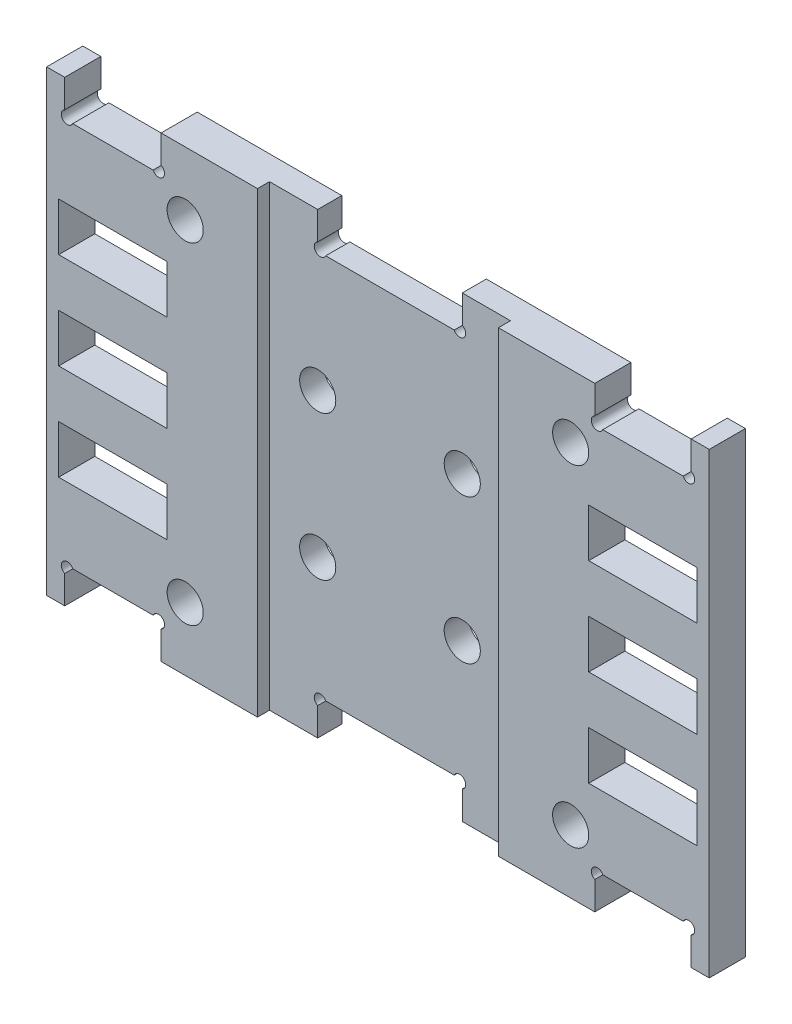
SolidWorks part; units mm, degrees
ref_plane "前视基准面" through (0, 0, 0) normal (0, 0, 1) x (1, 0, 0)
ref_plane "上视基准面" through (0, 0, 0) normal (0, 1, 0) x (1, 0, 0)
ref_plane "右视基准面" through (0, 0, 0) normal (1, 0, 0) x (0, 0, -1)
sketch "草图1" plane through (0, 0, 0) normal (0, 0, 1) x (1, 0, 0)
  line L1 (-27.5, 19) -> (27.5, 19)
  line L2 (-27.5, 19) -> (-27.5, -19)
  line L3 (-27.5, -19) -> (27.5, -19)
  line L4 (27.5, 19) -> (27.5, -19)
  line L5 (-27.5, 19) -> (27.5, -19) construction
  line L6 (-27.5, -19) -> (27.5, 19) construction
  point P0 (0, 0)
  dimension "D1" = 38
  dimension "D2" = 55
extrude "凸台-拉伸1" add sketch "草图1" along normal blind 3
sketch "草图2" plane through (0, 0, 3) normal (0, 0, 1) x (1, 0, 0)
  line L0 (-34.5256, 0) -> (42.1415, 0) construction
  line L1 (-10, -19) -> (-10, 19) construction
  line L2 (-27.5, -19) -> (27.5, -19) construction
  line L3 (27.5, 19) -> (-27.5, 19) construction
  line L4 (0, 26.7268) -> (0, -34.771) construction
  line L5 (10, -19) -> (10, 19) construction
  circle A0 centre (16, 13.75) radius 1.5
  circle A1 centre (16, -13.75) radius 1.5
  circle A2 centre (-16, 13.75) radius 1.5
  circle A3 centre (-16, -13.75) radius 1.5
  dimension "D1" = 13.75
  dimension "D2" = 3
  dimension "D3" = 10
  dimension "D4" = 6
extrude "切除-拉伸1" cut sketch "草图2" against normal blind 30
sketch "草图3" plane through (0, 0, 3) normal (0, 0, 1) x (1, 0, 0)
  line L0 (10, -19) -> (10, 19) construction
  line L1 (0, 26.7268) -> (0, -34.771) construction
  line L2 (-34.5256, 0) -> (42.1415, 0) construction
  line L3 (-10, -19) -> (-10, 19) construction
  line L4 (10, -19) -> (10, 19) construction
  line L5 (0, 26.7268) -> (0, -34.771) construction
  line L6 (-34.5256, 0) -> (42.1415, 0) construction
  line L7 (-10, -19) -> (-10, 19) construction
  line L8 (27.5, 19) -> (-27.5, 19) construction
  line L9 (27.5, -19) -> (27.5, 19) construction
  line L12 (18, 19) -> (26, 19)
  line L13 (18, 19) -> (18, 16)
  line L14 (18, 16) -> (26, 16)
  line L15 (26, 19) -> (26, 16)
  line L17 (26, -19) -> (26, -16)
  line L18 (18, -16) -> (26, -16)
  line L19 (18, -19) -> (18, -16)
  line L20 (18, -19) -> (26, -19)
  line L21 (-26, 19) -> (-26, 16)
  line L22 (-18, 16) -> (-26, 16)
  line L23 (-18, 19) -> (-18, 16)
  line L24 (-18, 19) -> (-26, 19)
  line L25 (-18, -19) -> (-26, -19)
  line L26 (-18, -19) -> (-18, -16)
  line L27 (-18, -16) -> (-26, -16)
  line L28 (-26, -19) -> (-26, -16)
  circle A0 centre (16, 13.75) radius 4 construction
  dimension "D1" = 8
  dimension "D2" = 1.5
  dimension "D3" = 8
  dimension "D4" = 3
extrude "切除-拉伸2" cut sketch "草图3" against normal blind 30
sketch "草图4" plane through (0, 0, 3) normal (0, 0, 1) x (1, 0, 0)
  line L0 (10, -19) -> (10, 19) construction
  line L1 (-10, -19) -> (-10, 19) construction
  line L2 (10, -19) -> (10, 19)
  line L3 (-10, -19) -> (-10, 19)
  line L4 (-10, -19) -> (10, -19)
  line L5 (-10, 19) -> (10, 19)
extrude "切除-拉伸3" cut sketch "草图4" against normal blind 1
sketch "草图5" plane through (0, 0, 3) normal (0, 0, 1) x (1, 0, 0)
  line L0 (36.0158, 0) -> (-43.2134, 0) construction
  line L1 (0, -26.7679) -> (0, 34.1112) construction
  line L2 (22, -14) -> (22, 14) construction
  line L3 (26.5, 6) -> (17.5, 6)
  line L4 (26.5, -2) -> (17.5, -2)
  line L5 (26.5, -2) -> (26.5, 2)
  line L6 (26.5, 2) -> (17.5, 2)
  line L7 (17.5, -2) -> (17.5, 2)
  line L8 (26.5, -2) -> (17.5, 2) construction
  line L9 (26.5, 2) -> (17.5, -2) construction
  line L10 (26.5, 6) -> (26.5, 10)
  line L11 (26.5, 6) -> (17.5, 10) construction
  line L12 (26.5, 10) -> (17.5, 6) construction
  line L13 (26.5, 10) -> (17.5, 10)
  line L14 (17.5, 6) -> (17.5, 10)
  line L15 (26.5, -10) -> (17.5, -10)
  line L16 (26.5, -10) -> (17.5, -6) construction
  line L17 (26.5, -6) -> (17.5, -6)
  line L18 (17.5, -10) -> (17.5, -6)
  line L19 (26.5, -6) -> (17.5, -10) construction
  line L20 (26.5, -10) -> (26.5, -6)
  line L21 (-26.5, -6) -> (-17.5, -10) construction
  line L22 (-26.5, -10) -> (-17.5, -6) construction
  line L23 (-26.5, 10) -> (-17.5, 6) construction
  line L24 (-26.5, 6) -> (-17.5, 10) construction
  line L25 (-26.5, 2) -> (-17.5, -2) construction
  line L26 (-26.5, -2) -> (-17.5, 2) construction
  line L27 (-26.5, -10) -> (-26.5, -6)
  line L28 (-17.5, -10) -> (-17.5, -6)
  line L29 (-26.5, -6) -> (-17.5, -6)
  line L30 (-26.5, -10) -> (-17.5, -10)
  line L31 (-17.5, 6) -> (-17.5, 10)
  line L32 (-26.5, 10) -> (-17.5, 10)
  line L33 (-26.5, 6) -> (-26.5, 10)
  line L34 (-17.5, -2) -> (-17.5, 2)
  line L35 (-26.5, 2) -> (-17.5, 2)
  line L36 (-26.5, -2) -> (-26.5, 2)
  line L37 (-26.5, -2) -> (-17.5, -2)
  line L38 (-26.5, 6) -> (-17.5, 6)
  point P9 (22, 0)
  point P14 (15, -8)
  point P35 (-15, -8)
  point P36 (-22, 0)
  dimension "D1" = 9
  dimension "D2" = 4
  dimension "D5" = 44
  dimension "D3" = 2
  dimension "D4" = 2
extrude "切除-拉伸4" cut sketch "草图5" against normal blind 10
sketch "草图6" plane through (0, 0, 2) normal (0, 0, 1) x (1, 0, 0)
  line L0 (10, 19) -> (-10, 19) construction
  line L1 (6, 16) -> (-6, 16)
  line L2 (6, 16) -> (6, 19)
  line L3 (6, 19) -> (-6, 19)
  line L4 (-6, 16) -> (-6, 19)
  line L5 (6, 16) -> (-6, 19) construction
  line L6 (6, 19) -> (-6, 16) construction
  line L7 (40.4069, 0) -> (-41.1435, 0) construction
  line L8 (6, -19) -> (-6, -16) construction
  line L9 (6, -16) -> (-6, -19) construction
  line L10 (-6, -16) -> (-6, -19)
  line L11 (6, -19) -> (-6, -19)
  line L12 (6, -16) -> (6, -19)
  line L13 (6, -16) -> (-6, -16)
  point P0 (0, 17.5)
  point P14 (0, -17.5)
  dimension "D1" = 3
  dimension "D2" = 12
extrude "切除-拉伸5" cut sketch "草图6" against normal blind 10
sketch "草图8" plane through (0, 0, 2) normal (0, 0, 1) x (1, 0, 0)
  line L0 (35.8146, 0) -> (-38.9097, 0) construction
  line L1 (0, -25.4239) -> (0, 33.2722) construction
  circle A0 centre (6, -6) radius 1.5
  circle A1 centre (6, 6) radius 1.5
  circle A2 centre (-6, 6) radius 1.5
  circle A3 centre (-6, -6) radius 1.5
  dimension "D1" = 6
  dimension "D3" = 3
  dimension "D2" = 6
extrude "切除-拉伸6" cut sketch "草图8" against normal blind 10
sketch "草图9" plane through (0, 0, 3) normal (0, 0, 1) x (1, 0, 0)
  line L0 (26, -16) -> (21.2547, -20.7453) construction
  line L1 (26, -16) -> (18, -16) construction
  line L2 (26, -16) -> (18, -16) construction
  line L3 (26, -19) -> (26, -16) construction
  line L4 (22, -16) -> (22, 6) construction
  line L5 (17.5, 6) -> (26.5, 6) construction
  line L6 (32.6576, 0) -> (-31.0257, 0) construction
  line L7 (26, 16) -> (18, 16) construction
  line L8 (0, -22.545) -> (0, 25.0951) construction
  line L9 (-26, 16) -> (-18, 16) construction
  line L10 (-22, -16) -> (-22, 6) construction
  line L11 (-26, -16) -> (-18, -16) construction
  line L12 (6, -16) -> (2.9183, -19.0817) construction
  line L13 (6, -16) -> (-6, -16) construction
  circle A0 centre (25.7879, -16.2121) radius 0.5
  circle A1 centre (18.2121, -16.2121) radius 0.5
  circle A2 centre (18.2121, 16.2121) radius 0.5
  circle A3 centre (25.7879, 16.2121) radius 0.5
  circle A4 centre (-25.7879, 16.2121) radius 0.5
  circle A5 centre (-18.2121, 16.2121) radius 0.5
  circle A6 centre (-18.2121, -16.2121) radius 0.5
  circle A7 centre (-25.7879, -16.2121) radius 0.5
  circle A8 centre (5.7879, -16.2121) radius 0.5
  circle A9 centre (-5.7879, -16.2121) radius 0.5
  circle A10 centre (-5.7879, 16.2121) radius 0.5
  circle A11 centre (5.7879, 16.2121) radius 0.5
  point P9 (26, -16.6649)
  point P23 (26, 16.6649)
  point P40 (-26, 16.6649)
  point P41 (-26, -16.6649)
  dimension "D1" = 1
  dimension "D4" = 45
  dimension "D2" = 45
  dimension "D3" = 0.3
  dimension "D5" = 0.3
extrude "切除-拉伸7" cut sketch "草图9" against normal through all
